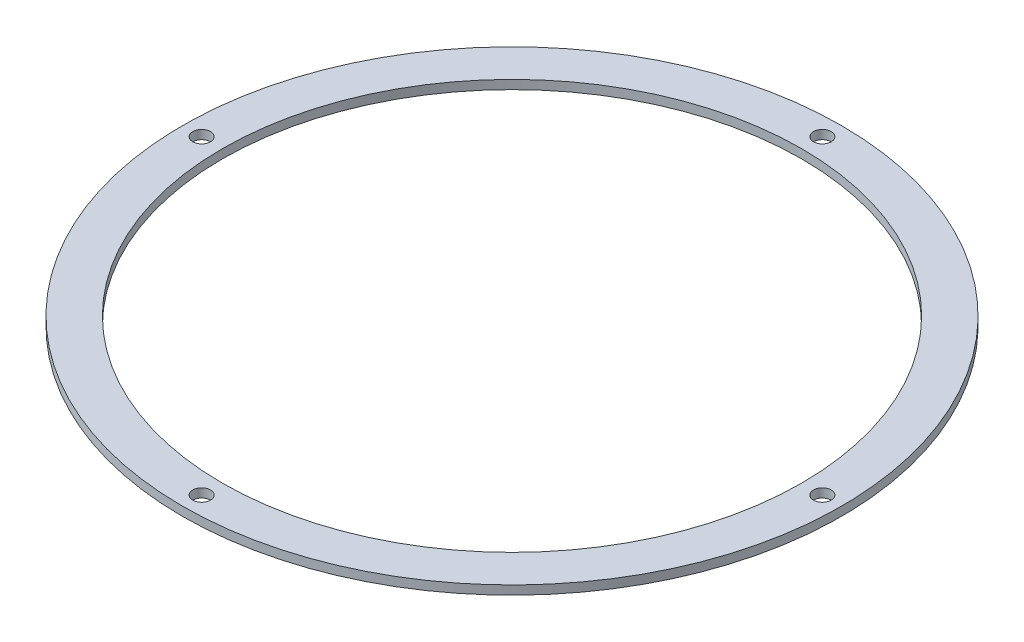
SolidWorks part; units mm, degrees
ref_plane "Front Plane" through (0, 0, 0) normal (0, 0, 1) x (1, 0, 0)
ref_plane "Top Plane" through (0, 0, 0) normal (0, 1, 0) x (1, 0, 0)
ref_plane "Right Plane" through (0, 0, 0) normal (1, 0, 0) x (0, 0, -1)
sketch "Sketch1" plane through (0, 0, 0) normal (0, 1, 0) x (1, 0, 0)
  circle A0 centre (0, 0) radius 98
  circle A1 centre (0, 0) radius 111.5
  dimension "D1" = 223
  dimension "D2" = 196
extrude "Boss-Extrude1" add sketch "Sketch1" along normal blind 3
sketch "Sketch2" plane through (0, 3, 0) normal (0, 1, 0) x (1, 0, 0)
  circle A0 centre (0, 105) radius 3
  circle A1 centre (105, 0) radius 3
  circle A2 centre (0, -105) radius 3
  circle A3 centre (-105, 0) radius 3
  circle A4 centre (0, 0) radius 105 construction
  point P8 (0, 0)
  point P9 (0, 0)
  point P10 (0, 0)
  point P11 (0, 0)
  point P12 (0, 0)
  dimension "D1" = 6
  dimension "D2" = 6
  dimension "D3" = 6
  dimension "D4" = 6
  dimension "D5" = 210
extrude "Cut-Extrude1" cut sketch "Sketch2" against normal through all
